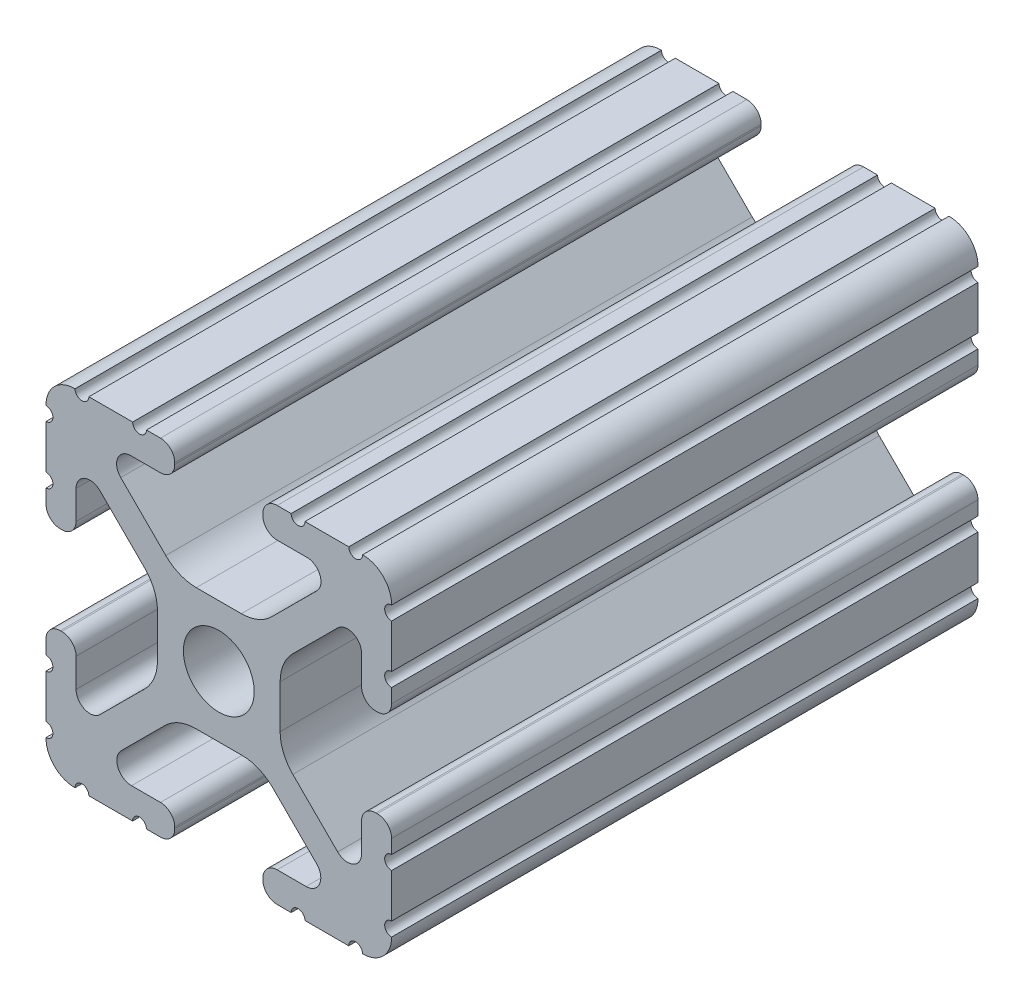
SolidWorks part; units mm, degrees
ref_plane "Front Plane" through (0, 0, 0) normal (0, 0, 1) x (1, 0, 0)
ref_plane "Top Plane" through (0, 0, 0) normal (0, 1, 0) x (1, 0, 0)
ref_plane "Right Plane" through (0, 0, 0) normal (1, 0, 0) x (0, 0, -1)
sketch "Sketch1" plane through (0, 0, 0) normal (0, 0, 1) x (1, 0, 0)
  line L88 (-7.1797, -8.6452) -> (-3.9523, -5.4237)
  line L89 (-1.7093, -4.4958) -> (1.7093, -4.4958)
  line L90 (3.9523, -5.4237) -> (7.1797, -8.6452)
  line L91 (6.4164, -10.4902) -> (4.2875, -10.4902)
  line L92 (3.2385, -11.5392) -> (3.2385, -11.651)
  line L93 (4.2875, -12.7) -> (5.3171, -12.7)
  line L94 (6.3331, -12.7) -> (9.5504, -12.7)
  line L95 (12.7, -9.5504) -> (12.7, -6.3331)
  line L96 (12.7, -5.3171) -> (12.7, -4.2875)
  line L97 (11.651, -3.2385) -> (11.5392, -3.2385)
  line L98 (10.4902, -4.2875) -> (10.4902, -6.4021)
  line L99 (8.7371, -7.1294) -> (5.441, -3.8408)
  line L100 (4.5085, -1.5932) -> (4.5085, 1.5932)
  line L101 (5.441, 3.8408) -> (8.7371, 7.1294)
  line L102 (10.4902, 6.4021) -> (10.4902, 4.2875)
  line L103 (11.5392, 3.2385) -> (11.651, 3.2385)
  line L104 (12.7, 4.2875) -> (12.7, 5.3171)
  line L105 (12.7, 6.3331) -> (12.7, 9.5504)
  line L106 (9.5504, 12.7) -> (6.3331, 12.7)
  line L107 (5.3171, 12.7) -> (4.2875, 12.7)
  line L108 (3.2385, 11.651) -> (3.2385, 11.5392)
  line L109 (4.2875, 10.4902) -> (6.4768, 10.4902)
  line L110 (7.207, 8.7244) -> (3.8983, 5.4232)
  line L111 (1.6558, 4.4958) -> (-1.6558, 4.4958)
  line L112 (-3.8983, 5.4232) -> (-7.207, 8.7244)
  line L113 (-6.4768, 10.4902) -> (-4.2875, 10.4902)
  line L114 (-3.2385, 11.5392) -> (-3.2385, 11.651)
  line L115 (-4.2875, 12.7) -> (-5.3171, 12.7)
  line L116 (-6.3331, 12.7) -> (-9.5504, 12.7)
  line L117 (-12.7, 9.5504) -> (-12.7, 6.3331)
  line L118 (-12.7, 5.3171) -> (-12.7, 4.2875)
  line L119 (-11.651, 3.2385) -> (-11.5392, 3.2385)
  line L120 (-10.4902, 4.2875) -> (-10.4902, 6.4021)
  line L121 (-8.7371, 7.1294) -> (-5.441, 3.8408)
  line L122 (-4.5085, 1.5932) -> (-4.5085, -1.5932)
  line L123 (-5.441, -3.8408) -> (-8.7371, -7.1294)
  line L124 (-10.4902, -6.4021) -> (-10.4902, -4.2875)
  line L125 (-11.5392, -3.2385) -> (-11.651, -3.2385)
  line L126 (-12.7, -4.2875) -> (-12.7, -5.3171)
  line L127 (-12.7, -6.3331) -> (-12.7, -9.5504)
  line L128 (-9.5504, -12.7) -> (-6.3331, -12.7)
  line L129 (-5.3171, -12.7) -> (-4.2875, -12.7)
  line L130 (-3.2385, -11.651) -> (-3.2385, -11.5392)
  line L131 (-4.2875, -10.4902) -> (-6.4164, -10.4902)
  circle A1 centre (0, 0) radius 2.6035
  arc A104 (-7.1797, -8.6452) -> (-6.4164, -10.4902) centre (-6.4164, -9.4098) ccw
  arc A105 (-1.7093, -4.4958) -> (-3.9523, -5.4237) centre (-1.7093, -7.6708) ccw
  arc A106 (3.9523, -5.4237) -> (1.7093, -4.4958) centre (1.7093, -7.6708) ccw
  arc A107 (6.4164, -10.4902) -> (7.1797, -8.6452) centre (6.4164, -9.4098) ccw
  arc A108 (4.2875, -10.4902) -> (3.2385, -11.5392) centre (4.2875, -11.5392) ccw
  arc A109 (3.2385, -11.651) -> (4.2875, -12.7) centre (4.2875, -11.651) ccw
  arc A110 (6.3331, -12.7) -> (5.3171, -12.7) centre (5.8251, -12.7) ccw
  arc A111 (10.5664, -12.6998) -> (9.5504, -12.7) centre (10.0584, -12.7) ccw
  arc A112 (10.5664, -12.6998) -> (12.6998, -10.5664) centre (10.5918, -10.5918) ccw
  arc A113 (12.7, -9.5504) -> (12.6998, -10.5664) centre (12.7, -10.0584) ccw
  arc A114 (12.7, -5.3171) -> (12.7, -6.3331) centre (12.7, -5.8251) ccw
  arc A115 (12.7, -4.2875) -> (11.651, -3.2385) centre (11.651, -4.2875) ccw
  arc A116 (11.5392, -3.2385) -> (10.4902, -4.2875) centre (11.5392, -4.2875) ccw
  arc A117 (8.7371, -7.1294) -> (10.4902, -6.4021) centre (9.4628, -6.4021) ccw
  arc A118 (4.5085, -1.5932) -> (5.441, -3.8408) centre (7.6835, -1.5932) ccw
  arc A119 (5.441, 3.8408) -> (4.5085, 1.5932) centre (7.6835, 1.5932) ccw
  arc A120 (10.4902, 6.4021) -> (8.7371, 7.1294) centre (9.4628, 6.4021) ccw
  arc A121 (10.4902, 4.2875) -> (11.5392, 3.2385) centre (11.5392, 4.2875) ccw
  arc A122 (11.651, 3.2385) -> (12.7, 4.2875) centre (11.651, 4.2875) ccw
  arc A123 (12.7, 6.3331) -> (12.7, 5.3171) centre (12.7, 5.8251) ccw
  arc A124 (12.6998, 10.5664) -> (12.7, 9.5504) centre (12.7, 10.0584) ccw
  arc A125 (12.6998, 10.5664) -> (10.5664, 12.6998) centre (10.5918, 10.5918) ccw
  arc A126 (9.5504, 12.7) -> (10.5664, 12.6998) centre (10.0584, 12.7) ccw
  arc A127 (5.3171, 12.7) -> (6.3331, 12.7) centre (5.8251, 12.7) ccw
  arc A128 (4.2875, 12.7) -> (3.2385, 11.651) centre (4.2875, 11.651) ccw
  arc A129 (3.2385, 11.5392) -> (4.2875, 10.4902) centre (4.2875, 11.5392) ccw
  arc A130 (7.207, 8.7244) -> (6.4768, 10.4902) centre (6.4768, 9.4563) ccw
  arc A131 (1.6558, 4.4958) -> (3.8983, 5.4232) centre (1.6558, 7.6708) ccw
  arc A132 (-3.8983, 5.4232) -> (-1.6558, 4.4958) centre (-1.6558, 7.6708) ccw
  arc A133 (-6.4768, 10.4902) -> (-7.207, 8.7244) centre (-6.4768, 9.4563) ccw
  arc A134 (-4.2875, 10.4902) -> (-3.2385, 11.5392) centre (-4.2875, 11.5392) ccw
  arc A135 (-3.2385, 11.651) -> (-4.2875, 12.7) centre (-4.2875, 11.651) ccw
  arc A136 (-6.3331, 12.7) -> (-5.3171, 12.7) centre (-5.8251, 12.7) ccw
  arc A137 (-10.5664, 12.6998) -> (-9.5504, 12.7) centre (-10.0584, 12.7) ccw
  arc A138 (-10.5664, 12.6998) -> (-12.6998, 10.5664) centre (-10.5918, 10.5918) ccw
  arc A139 (-12.7, 9.5504) -> (-12.6998, 10.5664) centre (-12.7, 10.0584) ccw
  arc A140 (-12.7, 5.3171) -> (-12.7, 6.3331) centre (-12.7, 5.8251) ccw
  arc A141 (-12.7, 4.2875) -> (-11.651, 3.2385) centre (-11.651, 4.2875) ccw
  arc A142 (-11.5392, 3.2385) -> (-10.4902, 4.2875) centre (-11.5392, 4.2875) ccw
  arc A143 (-8.7371, 7.1294) -> (-10.4902, 6.4021) centre (-9.4628, 6.4021) ccw
  arc A144 (-4.5085, 1.5932) -> (-5.441, 3.8408) centre (-7.6835, 1.5932) ccw
  arc A145 (-5.441, -3.8408) -> (-4.5085, -1.5932) centre (-7.6835, -1.5932) ccw
  arc A146 (-10.4902, -6.4021) -> (-8.7371, -7.1294) centre (-9.4628, -6.4021) ccw
  arc A147 (-10.4902, -4.2875) -> (-11.5392, -3.2385) centre (-11.5392, -4.2875) ccw
  arc A148 (-11.651, -3.2385) -> (-12.7, -4.2875) centre (-11.651, -4.2875) ccw
  arc A149 (-12.7, -6.3331) -> (-12.7, -5.3171) centre (-12.7, -5.8251) ccw
  arc A150 (-12.6998, -10.5664) -> (-12.7, -9.5504) centre (-12.7, -10.0584) ccw
  arc A151 (-12.6998, -10.5664) -> (-10.5664, -12.6998) centre (-10.5918, -10.5918) ccw
  arc A152 (-9.5504, -12.7) -> (-10.5664, -12.6998) centre (-10.0584, -12.7) ccw
  arc A153 (-5.3171, -12.7) -> (-6.3331, -12.7) centre (-5.8251, -12.7) ccw
  arc A154 (-4.2875, -12.7) -> (-3.2385, -11.651) centre (-4.2875, -11.651) ccw
  arc A155 (-3.2385, -11.5392) -> (-4.2875, -10.4902) centre (-4.2875, -11.5392) ccw
extrude "Boss-Extrude1" add sketch "Sketch1" along normal mid plane 43.1
